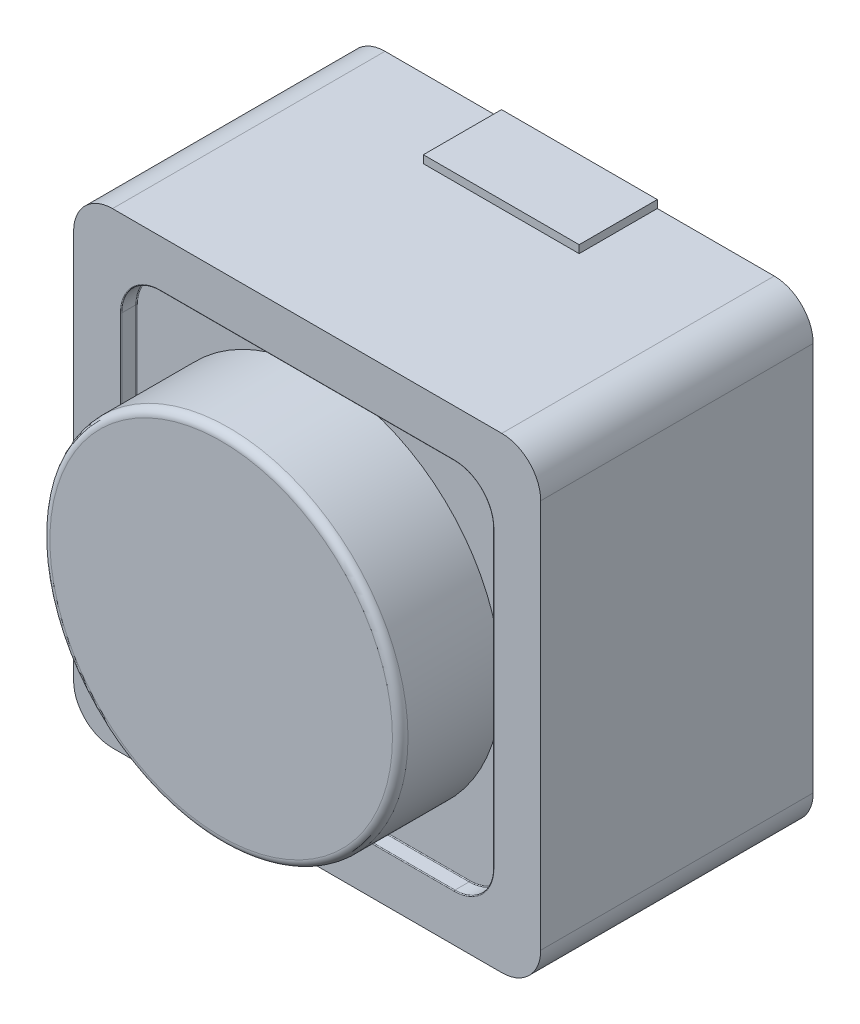
SolidWorks part; units mm, degrees
material "Plastique personnalisé"
ref_plane "Plan de face" through (0, 0, 0) normal (0, 0, 1) x (1, 0, 0)
ref_plane "Plan de dessus" through (0, 0, 0) normal (0, 1, 0) x (1, 0, 0)
ref_plane "Plan de droite" through (0, 0, 0) normal (1, 0, 0) x (0, 0, -1)
sketch "Esquisse1" plane through (0, 0, 0) normal (0, 0, 1) x (1, 0, 0)
  line L1 (0.5, 0) -> (5.5, 0)
  line L2 (0, 0.5) -> (0, 5.5)
  line L3 (0.5, 6) -> (5.5, 6)
  line L4 (6, 0.5) -> (6, 5.5)
  arc A0 (5.5, 0) -> (6, 0.5) centre (5.5, 0.5) ccw
  arc A1 (0.5, 0) -> (0, 0.5) centre (0.5, 0.5) cw
  arc A2 (0, 5.5) -> (0.5, 6) centre (0.5, 5.5) cw
  arc A3 (5.5, 6) -> (6, 5.5) centre (5.5, 5.5) cw
  point P7 (6, 0)
  point P10 (0, 0)
  point P13 (0, 6)
  point P16 (6, 6)
  dimension "D3" = 0.5
  dimension "D1" = 6
  dimension "D2" = 6
extrude "Boss.-Extru.1" add sketch "Esquisse1" along normal blind 3.5
sketch "Esquisse2" plane through (0, 0, 3.5) normal (0, 0, 1) x (1, 0, 0)
  line L0 (6, 3) -> (0, 3) construction
  line L1 (6, 0.5) -> (6, 5.5) construction
  line L2 (0, 5.5) -> (0, 0.5) construction
  line L3 (3, 6) -> (3, 0) construction
  line L4 (5.5, 6) -> (0.5, 6) construction
  line L5 (0.5, 0) -> (5.5, 0) construction
  line L7 (1.11, 0.61) -> (4.89, 0.61)
  line L8 (0.61, 1.11) -> (0.61, 4.89)
  line L9 (1.11, 5.39) -> (4.89, 5.39)
  line L10 (5.39, 1.11) -> (5.39, 4.89)
  line L11 (0.61, 0.61) -> (5.39, 5.39) construction
  line L12 (0.61, 5.39) -> (5.39, 0.61) construction
  arc A0 (4.89, 0.61) -> (5.39, 1.11) centre (4.89, 1.11) ccw
  arc A1 (1.11, 0.61) -> (0.61, 1.11) centre (1.11, 1.11) cw
  arc A2 (4.89, 5.39) -> (5.39, 4.89) centre (4.89, 4.89) cw
  arc A3 (0.61, 4.89) -> (1.11, 5.39) centre (1.11, 4.89) cw
  point P12 (3, 3)
  dimension "D3" = 0.5
  dimension "D1" = 4.78
  dimension "D2" = 4.78
extrude "Enlèv. mat.-Extru.1" cut sketch "Esquisse2" against normal blind 0.2
sketch "Esquisse3" plane through (0, 0, 3.3) normal (0, 0, 1) x (1, 0, 0)
  circle A0 centre (2.9956, 3.0113) radius 2.3
extrude "Boss.-Extru.2" add sketch "Esquisse3" along normal blind 1.3
fillet "Congé1" radius 0.1 1 edges at (5.2956, 3.0113, 4.6)
fillet "Congé2" radius 0.01 16 edges at (3, 0.61, 3.5) (3, 5.39, 3.5) (5.2436, 5.2436, 3.3) (5.39, 3, 3.3) (5.2436, 0.7564, 3.3) (0.7564, 0.7564, 3.3) (0.61, 3, 3.3) (0.7564, 5.2436, 3.3) (0.7564, 5.2436, 3.5) (0.61, 3, 3.5) (0.7564, 0.7564, 3.5) (3, 0.61, 3.3) (5.2436, 0.7564, 3.5) (5.39, 3, 3.5) (5.2436, 5.2436, 3.5) (3, 5.39, 3.3)
sketch "Esquisse4" plane through (0, 0, 0) normal (0, -1, 0) x (1, 0, 0)
  line L0 (3, 0) -> (3.998, 0) construction
  line L1 (0.5, 0) -> (5.5, 0) construction
  line L3 (3.998, 0) -> (1.9995, 0)
  line L4 (3.998, 0) -> (3.998, 1.0048)
  line L5 (3.998, 1.0048) -> (1.9995, 1.0048)
  line L6 (1.9995, 0) -> (1.9995, 1.0048)
extrude "Boss.-Extru.3" add sketch "Esquisse4" along normal blind 0.1
sketch "Esquisse5" plane through (0, 6, 0) normal (0, 1, 0) x (1, 0, 0)
  line L1 (3.998, 0) -> (1.9969, 0)
  line L2 (3.998, 0) -> (3.998, -1.0041)
  line L3 (3.998, -1.0041) -> (1.9969, -1.0041)
  line L4 (1.9969, 0) -> (1.9969, -1.0041)
extrude "Boss.-Extru.4" add sketch "Esquisse5" along normal blind 0.1
